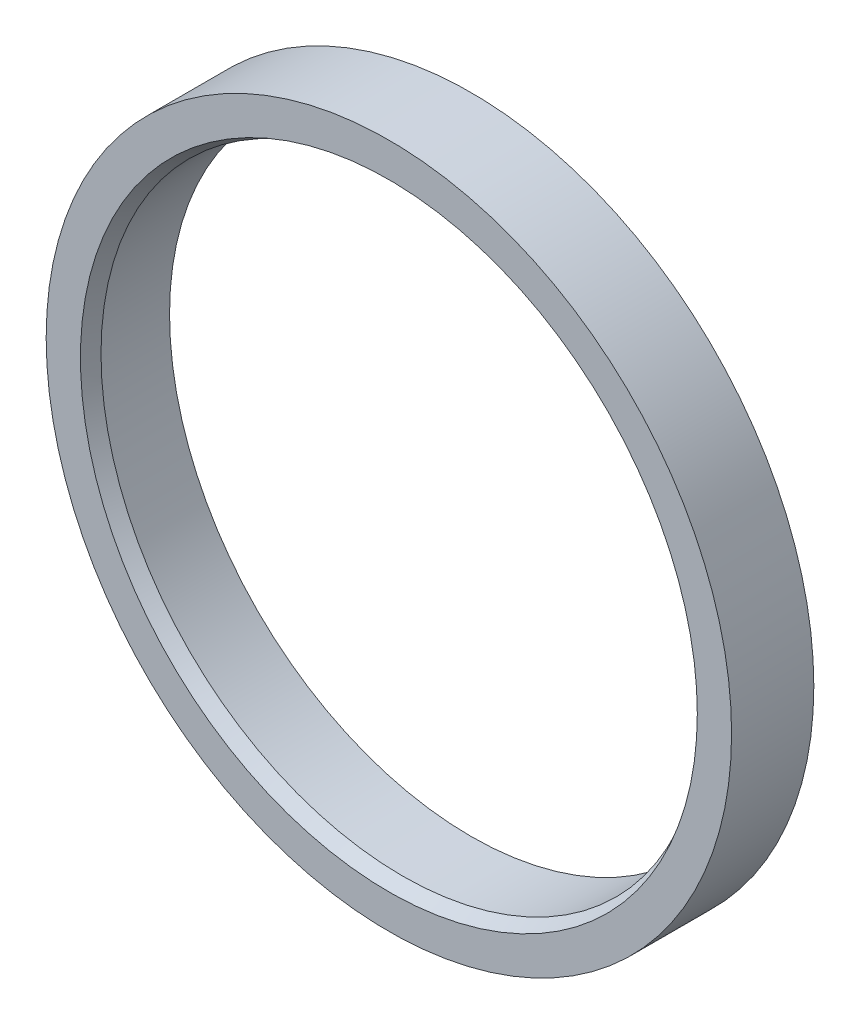
SolidWorks part; units mm, degrees
material "6061-T6 (SS)"
ref_plane "Front Plane" through (0, 0, 0) normal (0, 0, 1) x (1, 0, 0)
ref_plane "Top Plane" through (0, 0, 0) normal (0, 1, 0) x (1, 0, 0)
ref_plane "Right Plane" through (0, 0, 0) normal (1, 0, 0) x (0, 0, -1)
sketch "Sketch2" plane through (0, 0, 0) normal (1, 0, 0) x (0, 0, -1)
  line L0 (0, 0) -> (44.2866, 0) construction
  line L1 (0, 69.85) -> (19.05, 69.85)
  line L2 (0, 69.85) -> (0, 79.375)
  line L3 (0, 71.4375) -> (3.175, 69.85)
  line L5 (0, 79.375) -> (19.05, 79.375)
  line L6 (19.05, 79.375) -> (19.05, 76.2)
  line L7 (19.05, 76.2) -> (9.525, 76.2)
  line L8 (9.525, 76.2) -> (9.525, 72.2313)
  line L9 (9.525, 72.2313) -> (19.05, 72.2313)
  line L10 (19.05, 72.2313) -> (19.05, 69.85)
  dimension "D1" = 144.4625
  dimension "D2" = 139.7
  dimension "D3" = 152.4
  dimension "D4" = 3.175
  dimension "D5" = 9.525
  dimension "D6" = 1.5875
  dimension "D7" = 19.05
  dimension "D8" = 3.175
revolve "Revolve1" add sketch "Sketch2" angle 360 about L0
